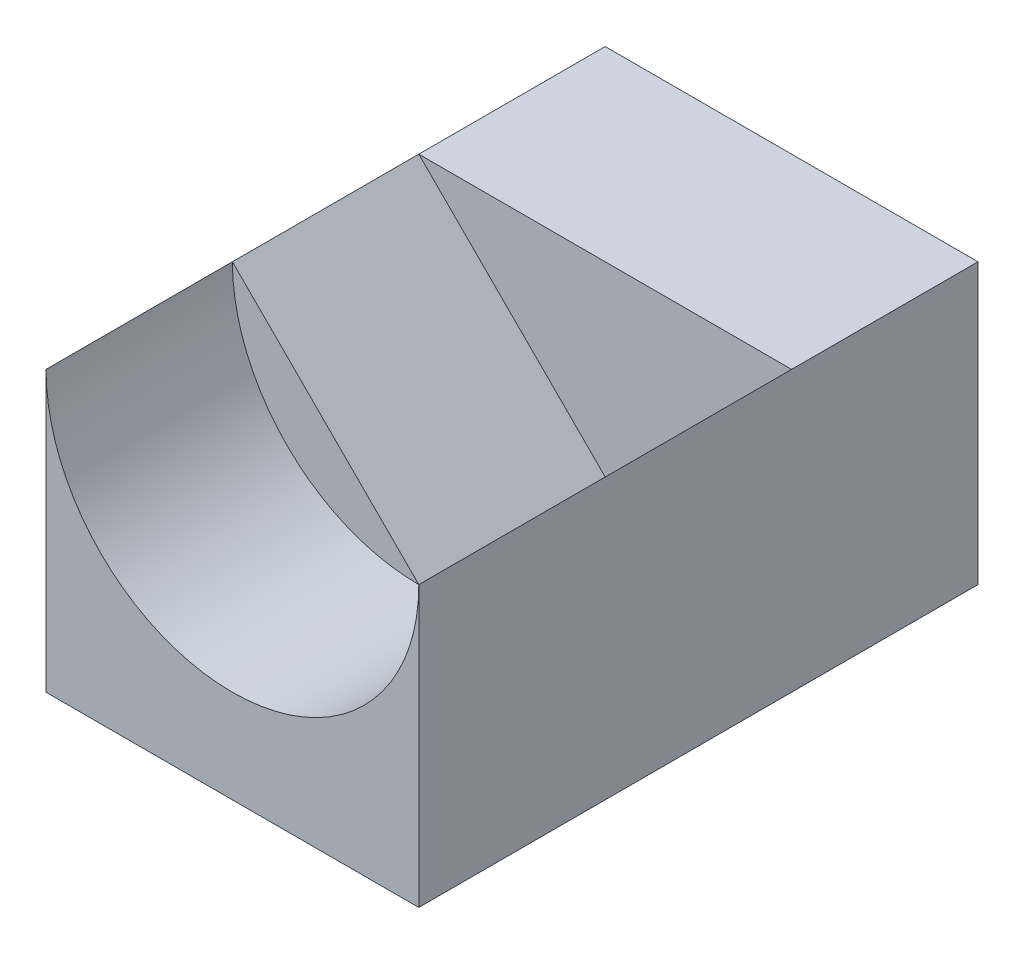
SolidWorks part; units mm, degrees
ref_plane "前基準面" through (0, 0, 0) normal (0, 0, 1) x (1, 0, 0)
ref_plane "上基準面" through (0, 0, 0) normal (0, 1, 0) x (1, 0, 0)
ref_plane "右基準面" through (0, 0, 0) normal (1, 0, 0) x (0, 0, -1)
sketch "草圖1" plane through (0, 0, 0) normal (0, 1, 0) x (1, 0, 0)
  line L1 (10, 15) -> (-10, 15)
  line L2 (10, 15) -> (10, -15)
  line L3 (10, -15) -> (-10, -15)
  line L4 (-10, 15) -> (-10, -15)
  line L5 (10, 15) -> (-10, -15) construction
  line L6 (10, -15) -> (-10, 15) construction
  point P0 (0, 0)
  dimension "D1" = 30
  dimension "D2" = 20
extrude "填料-伸長1" add sketch "草圖1" along normal blind 15
sketch "草圖2" plane through (0, 0, 15) normal (0, 0, 1) x (1, 0, 0)
  line L0 (-10, 15) -> (10, 15) construction
  line L1 (10, 15) -> (-10, 15)
  arc A0 (-10, 15) -> (10, 15) centre (0, 15) ccw
extrude "除料-伸長1" cut sketch "草圖2" against normal blind 10 contours A0 L1
sketch "草圖3" plane through (0, 0, 5) normal (0, 0, 1) x (1, 0, 0)
  line L0 (-10, 15) -> (0, 5)
  line L1 (0, 5) -> (10, 15)
  line L2 (10, 15) -> (-10, 15)
  arc A0 (-10, 15) -> (10, 15) centre (0, 15) ccw construction
extrude "除料-伸長2" cut sketch "草圖3" against normal blind 10
